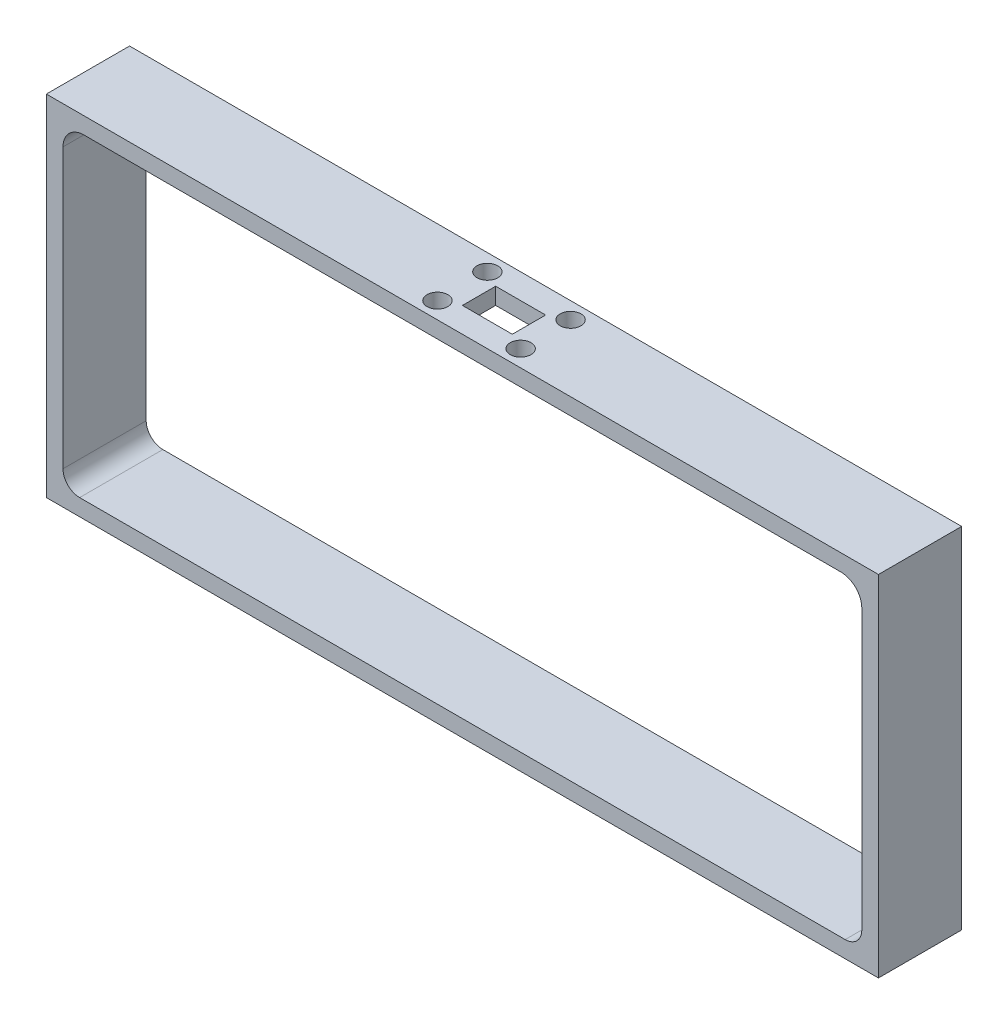
SolidWorks part; units mm, degrees
ref_plane "Front Plane" through (0, 0, 0) normal (0, 0, 1) x (1, 0, 0)
ref_plane "Top Plane" through (0, 0, 0) normal (0, 1, 0) x (1, 0, 0)
ref_plane "Right Plane" through (0, 0, 0) normal (1, 0, 0) x (0, 0, -1)
sketch "Sketch1" plane through (0, 0, 0) normal (0, 1, 0) x (1, 0, 0)
  line L0 (-63.5, 6.35) -> (-12.7, 6.35)
  line L1 (12.7, -6.35) -> (-12.7, -6.35)
  line L3 (12.7, 6.35) -> (-12.7, 6.35)
  line L5 (12.7, -6.35) -> (-12.7, 6.35) construction
  line L6 (12.7, 6.35) -> (-12.7, -6.35) construction
  line L8 (63.5, -6.35) -> (63.5, 6.35)
  line L10 (-63.5, -6.35) -> (-63.5, 6.35)
  line L11 (63.5, -6.35) -> (-63.5, 6.35) construction
  line L12 (63.5, 6.35) -> (-63.5, -6.35) construction
  line L13 (-63.5, -6.35) -> (-12.7, -6.35)
  line L14 (12.7, 6.35) -> (63.5, 6.35)
  line L15 (12.7, -6.35) -> (63.5, -6.35)
  line L16 (0, 0) -> (0, 6.35) construction
  line L17 (0, 0) -> (0, -6.35) construction
  line L18 (-63.5, 0) -> (0, 0) construction
  line L19 (0, 0) -> (63.5, 0) construction
  line L29 (3.81, -2.54) -> (-3.81, -2.54)
  line L30 (6.35, -3.81) -> (-6.35, -3.81) construction
  line L31 (6.35, -3.81) -> (6.35, 3.81) construction
  line L32 (6.35, 3.81) -> (-6.35, 3.81) construction
  line L33 (-6.35, -3.81) -> (-6.35, 3.81) construction
  line L34 (6.35, -3.81) -> (-6.35, 3.81) construction
  line L35 (6.35, 3.81) -> (-6.35, -3.81) construction
  line L36 (3.81, -2.54) -> (3.81, 2.54)
  line L37 (3.81, 2.54) -> (-3.81, 2.54)
  line L38 (-3.81, -2.54) -> (-3.81, 2.54)
  line L39 (3.81, -2.54) -> (-3.81, 2.54) construction
  line L40 (3.81, 2.54) -> (-3.81, -2.54) construction
  circle A0 centre (-6.35, 3.81) radius 1.5875
  circle A1 centre (6.35, 3.81) radius 1.5875
  circle A2 centre (6.35, -3.81) radius 1.5875
  circle A3 centre (-6.35, -3.81) radius 1.5875
  point P0 (0, 0)
  point P6 (0, 0)
  dimension "D10" = 3.175
  dimension "D1" = 12.7
  dimension "D2" = 127
  dimension "D3" = 12.7
  dimension "D4" = 7.62
  dimension "D5" = 5.08
  dimension "D7" = 25.4
  dimension "D8" = 12.7
  dimension "D9" = 7.62
extrude "Boss-Extrude1" add sketch "Sketch1" along normal blind 2.54
sketch "Sketch2" plane through (0, 0, 0) normal (0, -1, 0) x (1, 0, 0)
  line L0 (-63.5, 6.35) -> (-60.96, 6.35)
  line L1 (-63.5, 6.35) -> (63.5, 6.35) construction
  line L2 (-60.96, 6.35) -> (-60.96, -6.35)
  line L3 (63.5, -6.35) -> (-63.5, -6.35) construction
  line L4 (-60.96, -6.35) -> (-63.5, -6.35)
  line L5 (-63.5, -6.35) -> (-63.5, 6.35) construction
  line L6 (-63.5, -6.35) -> (-63.5, 6.35)
  line L7 (63.5, 6.35) -> (63.5, -6.35)
  line L8 (63.5, -6.35) -> (60.96, -6.35)
  line L9 (63.5, -6.35) -> (-63.5, -6.35) construction
  line L10 (60.96, -6.35) -> (60.96, 6.35)
  line L11 (-63.5, 6.35) -> (63.5, 6.35) construction
  line L12 (60.96, 6.35) -> (63.5, 6.35)
  dimension "D1" = 2.54
extrude "Boss-Extrude2" add sketch "Sketch2" along normal blind 50.8
sketch "Sketch3" plane through (0, -50.8, 0) normal (0, -1, 0) x (1, 0, 0)
  line L2 (-63.5, 6.35) -> (63.5, 6.35)
  line L17 (-63.5, 6.35) -> (-63.5, -6.35)
  line L38 (-63.5, -6.35) -> (63.5, -6.35)
  line L39 (63.5, 6.35) -> (63.5, -6.35)
extrude "Boss-Extrude3" add sketch "Sketch3" against normal blind 2.54
fillet "Fillet1" radius 2.54 2 edges at (60.96, -48.26, 0) (-60.96, -48.26, 0)
fillet "Fillet2" radius 3.175 2 edges at (60.96, 0, 0) (-60.96, 0, 0)
